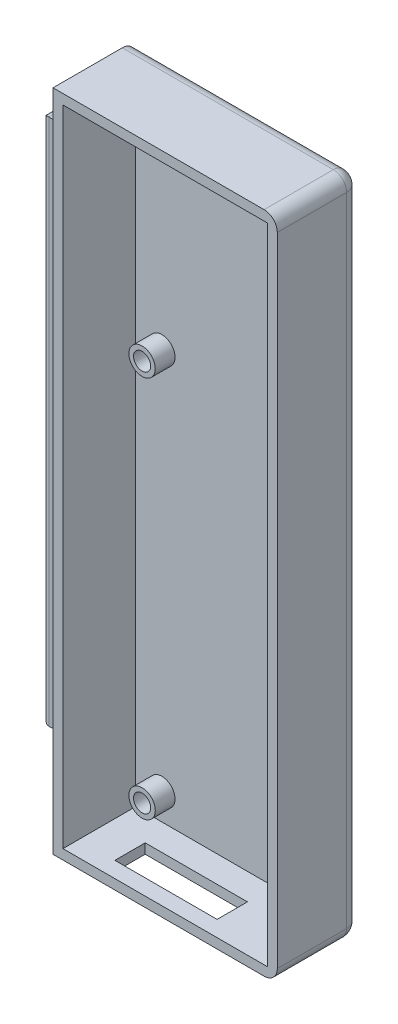
SolidWorks part; units mm, degrees
ref_plane "Plan de face" through (0, 0, 0) normal (0, 0, 1) x (1, 0, 0)
ref_plane "Plan de dessus" through (0, 0, 0) normal (0, 1, 0) x (1, 0, 0)
ref_plane "Plan de droite" through (0, 0, 0) normal (1, 0, 0) x (0, 0, -1)
sketch "Esquisse1" plane through (0, 0, 0) normal (0, 0, 1) x (1, 0, 0)
  line L1 (0, 0) -> (34, 0)
  line L2 (0, 0) -> (0, 100.65)
  line L3 (0, 100.65) -> (34, 100.65)
  line L4 (34, 0) -> (34, 100.65)
  dimension "D1" = 100.65
  dimension "D2" = 34
extrude "Boss.-Extru.1" add sketch "Esquisse1" along normal blind 12.5
sketch "Esquisse2" plane through (0, 0, 12.5) normal (0, 0, 1) x (1, 0, 0)
  line L0 (0, 100.65) -> (0, 0) construction
  line L1 (1.5, 99.15) -> (32.5, 99.15)
  line L2 (1.5, 99.15) -> (1.5, 1.5)
  line L3 (1.5, 1.5) -> (32.5, 1.5)
  line L4 (32.5, 99.15) -> (32.5, 1.5)
  line L5 (34, 0) -> (34, 100.65) construction
  line L6 (0, 0) -> (34, 0) construction
  line L7 (34, 100.65) -> (0, 100.65) construction
  dimension "D1" = 1.5
  dimension "D2" = 1.5
  dimension "D3" = 1.5
  dimension "D4" = 1.5
extrude "Enlèv. mat.-Extru.1" cut sketch "Esquisse2" against normal blind 11 contours L2 L1 L4 L3
sketch "RASP" plane through (0, 0, 1.5) normal (0, 0, 1) x (1, 0, 0)
  line L0 (1.5, 99.15) -> (1.5, 1.5) construction
  line L1 (2, 67) -> (32, 67)
  line L2 (2, 67) -> (2, 2)
  line L3 (2, 2) -> (32, 2)
  line L4 (32, 67) -> (32, 2)
  line L6 (1.5, 1.5) -> (32.5, 1.5) construction
  circle A0 centre (5.5, 5.5) radius 1.375
  circle A1 centre (28.5, 5.5) radius 1.375
  circle A2 centre (5.5, 63.5) radius 1.375
  circle A3 centre (28.5, 63.5) radius 1.375
  point P16 (32, 56)
  point P17 (32, 43.4)
  point P18 (0, 0)
  point P19 (0, 0)
  point P20 (0, 0)
  dimension "D5" = 2.75
  dimension "D6" = 2.75
  dimension "D11" = 2.75
  dimension "D12" = 2.75
  dimension "D1" = 30
  dimension "D2" = 65
  dimension "D3" = 0.5
  dimension "D4" = 0.5
  dimension "D7" = 23
  dimension "D8" = 3.5
  dimension "D9" = 3.5
  dimension "D10" = 3.5
  dimension "D13" = 23
  dimension "D14" = 3.5
  dimension "D15" = 3.5
  dimension "D16" = 3.5
  dimension "D17" = 54
  dimension "D18" = 41.4
sketch "Esquisse5" plane through (0, 0, 1.5) normal (0, 0, 1) x (1, 0, 0)
  circle A0 centre (5.5, 63.5) radius 2
  circle A1 centre (28.5, 63.5) radius 2
  circle A2 centre (5.5, 5.5) radius 2
  circle A3 centre (28.5, 5.5) radius 2
  dimension "D1" = 4
  dimension "D2" = 4
  dimension "D3" = 4
  dimension "D4" = 4
extrude "Boss.-Extru.4" add sketch "Esquisse5" along normal blind 3
sketch "Esquisse6" plane through (0, 0, 1.5) normal (0, 0, 1) x (1, 0, 0)
  circle A0 centre (5.5, 63.5) radius 1.2
  circle A1 centre (28.5, 63.5) radius 1.2
  circle A2 centre (5.5, 5.5) radius 1.2
  circle A3 centre (28.5, 5.5) radius 1.2
  dimension "D1" = 2.4
  dimension "D2" = 2.4
  dimension "D3" = 2.4
  dimension "D4" = 2.4
fillet "Congé2" radius 2 1 edges at (34, 0, 6.25)
fillet "Congé3" radius 2 1 edges at (34, 100.65, 6.25)
fillet "Congé4" radius 2 5 edges at (16, 0, 0) (33.4142, 0.5858, 0) (16, 100.65, 0) (33.4142, 100.0642, 0) (34, 50.325, 0)
sketch "Esquisse7" plane through (0, 0, 0) normal (-1, 0, 0) x (0, 0, 1)
  line L0 (0, 98.65) -> (0, 2) construction
  line L1 (3.25, 95.45) -> (10.75, 95.45)
  line L2 (3.25, 95.45) -> (3.25, 15.45)
  line L3 (3.25, 15.45) -> (10.75, 15.45)
  line L4 (10.75, 95.45) -> (10.75, 15.45)
  line L5 (12.5, 100.65) -> (2, 100.65) construction
  dimension "D1" = 3.25
  dimension "D2" = 5.2
  dimension "D3" = 7.5
  dimension "D4" = 80
extrude "Boss.-Extru.6" add sketch "Esquisse7" along normal blind 1
sketch "Esquisse9" plane through (-1, 0, 0) normal (-1, 0, 0) x (0, 0, 1)
  line L0 (3.25, 95.45) -> (3.25, 15.45) construction
  line L1 (2, 95.45) -> (11.45, 95.45)
  line L2 (2, 95.45) -> (2, 15.45)
  line L3 (2, 15.45) -> (11.45, 15.45)
  line L4 (11.45, 95.45) -> (11.45, 15.45)
  line L5 (10.75, 95.45) -> (3.25, 95.45) construction
  dimension "D1" = 80
  dimension "D2" = 0
  dimension "D3" = 9.45
  dimension "D4" = 1.25
extrude "Boss.-Extru.7" add sketch "Esquisse9" along normal blind 1.7
sketch "Esquisse11" plane through (0, 1.5, 0) normal (0, 1, 0) x (1, 0, 0)
  line L0 (1.5, -1.5) -> (32.5, -1.5) construction
  line L1 (22.4742, -10.1) -> (6.9742, -10.1)
  line L2 (22.4742, -10.1) -> (22.4742, -5.5)
  line L3 (22.4742, -5.5) -> (6.9742, -5.5)
  line L4 (6.9742, -10.1) -> (6.9742, -5.5)
  dimension "D1" = 15.5
  dimension "D2" = 4.6
  dimension "D3" = 4
extrude "Enlèv. mat.-Extru.3" cut sketch "Esquisse11" against normal blind 3 contours L2 L1 L4 L3
fillet "Congé7" radius 1 4 edges at (-2.7, 95.45, 6.725) (-2.7, 55.45, 2) (-2.7, 15.45, 6.725) (-2.7, 55.45, 11.45)
sketch "Esquisse12" plane through (0, 0, 4.5) normal (0, 0, 1) x (1, 0, 0)
  circle A0 centre (5.5, 63.5) radius 1.3
  circle A1 centre (28.5, 63.5) radius 1.3
  circle A2 centre (5.5, 5.5) radius 1.3
  circle A3 centre (28.5, 5.5) radius 1.3
  point P12 (0, 0)
extrude "Enlèv. mat.-Extru.5" cut sketch "Esquisse12" against normal blind 3
